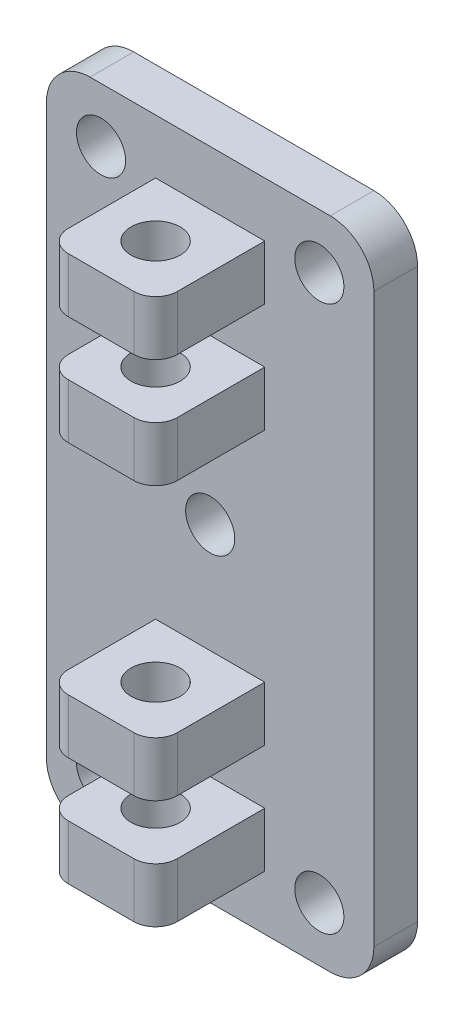
SolidWorks part; units mm, degrees
ref_plane "Plan de face" through (0, 0, 0) normal (0, 0, 1) x (1, 0, 0)
ref_plane "Plan de dessus" through (0, 0, 0) normal (0, 1, 0) x (1, 0, 0)
ref_plane "Plan de droite" through (0, 0, 0) normal (1, 0, 0) x (0, 0, -1)
sketch "Esquisse1" plane through (0, 0, 0) normal (0, 0, 1) x (1, 0, 0)
  line L1 (-30, 60) -> (0, 60)
  line L2 (-30, 60) -> (-30, 0)
  line L3 (-30, 0) -> (0, 0)
  line L4 (0, 60) -> (0, 0)
  dimension "D1" = 30
  dimension "D2" = 60
extrude "Boss.-Extru.1" add sketch "Esquisse1" along normal blind 4
sketch "Esquisse2" plane through (0, 0, 4) normal (0, 0, 1) x (1, 0, 0)
  line L0 (0, 0) -> (0, 60) construction
  line L1 (-20, 55) -> (-10, 55)
  line L2 (-20, 55) -> (-20, 50)
  line L3 (-20, 50) -> (-10, 50)
  line L4 (-10, 55) -> (-10, 50)
  line L5 (-20, 45) -> (-10, 45)
  line L6 (-20, 45) -> (-20, 40)
  line L7 (-20, 40) -> (-10, 40)
  line L8 (-10, 45) -> (-10, 40)
  line L9 (-20, 20) -> (-10, 20)
  line L10 (-20, 20) -> (-20, 15)
  line L11 (-20, 15) -> (-10, 15)
  line L12 (-10, 20) -> (-10, 15)
  line L13 (-20, 10) -> (-10, 10)
  line L14 (-20, 10) -> (-20, 5)
  line L15 (-20, 5) -> (-10, 5)
  line L16 (-10, 10) -> (-10, 5)
  line L17 (0, 60) -> (-30, 60) construction
  line L18 (-30, 0) -> (0, 0) construction
  dimension "D1" = 5
  dimension "D2" = 5
  dimension "D3" = 5
  dimension "D4" = 5
  dimension "D5" = 5
  dimension "D6" = 5
  dimension "D7" = 10
  dimension "D8" = 5
  dimension "D9" = 5
  dimension "D10" = 10
  dimension "D11" = 10
  dimension "D12" = 10
  dimension "D13" = 10
  dimension "D14" = 10
  dimension "D15" = 10
  dimension "D16" = 10
extrude "Boss.-Extru.2" add sketch "Esquisse2" along normal blind 10
sketch "Esquisse3" plane through (0, 5, 0) normal (0, -1, 0) x (1, 0, 0)
  line L0 (-10, 14) -> (-10, 4) construction
  line L1 (-20, 4) -> (-10, 4) construction
  circle A0 centre (-15, 9) radius 2.25
  dimension "D1" = 4.5
  dimension "D2" = 5
  dimension "D3" = 5
extrude "Enlèv. mat.-Extru.1" cut sketch "Esquisse3" against normal through all
fillet "Congé1" radius 2 8 edges at (-20, 52.5, 14) (-10, 52.5, 14) (-10, 42.5, 14) (-20, 42.5, 14) (-20, 17.5, 14) (-10, 17.5, 14) (-10, 7.5, 14) (-20, 7.5, 14)
fillet "Congé2" radius 4 4 edges at (0, 60, 2) (0, 0, 2) (-30, 0, 2) (-30, 60, 2)
sketch "Esquisse4" plane through (0, 0, 4) normal (0, 0, 1) x (1, 0, 0)
  line L0 (0, 4) -> (0, 56) construction
  line L1 (-4, 60) -> (-26, 60) construction
  line L2 (-30, 56) -> (-30, 4) construction
  line L3 (-26, 0) -> (-4, 0) construction
  circle A0 centre (-5, 55) radius 2.25
  circle A1 centre (-25, 55) radius 2.25
  circle A2 centre (-5, 5) radius 2.25
  circle A3 centre (-25, 5) radius 2.25
  circle A4 centre (-15, 30) radius 2.25
  dimension "D1" = 4.5
  dimension "D2" = 5
  dimension "D3" = 5
  dimension "D4" = 4.5
  dimension "D5" = 5
  dimension "D6" = 5
  dimension "D7" = 4.5
  dimension "D8" = 5
  dimension "D9" = 5
  dimension "D10" = 4.5
  dimension "D11" = 5
  dimension "D12" = 5
  dimension "D13" = 15
  dimension "D14" = 30
  dimension "D15" = 4.5
extrude "Enlèv. mat.-Extru.2" cut sketch "Esquisse4" against normal through all
